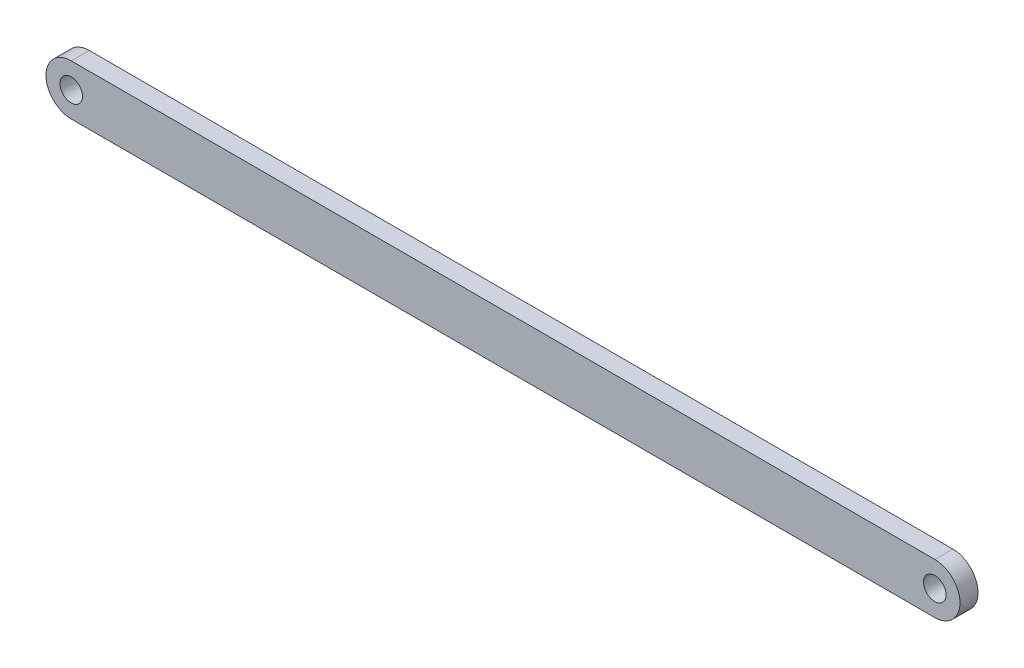
SolidWorks part; units mm, degrees
ref_plane "Front Plane" through (0, 0, 0) normal (0, 0, 1) x (1, 0, 0)
ref_plane "Top Plane" through (0, 0, 0) normal (0, 1, 0) x (1, 0, 0)
ref_plane "Right Plane" through (0, 0, 0) normal (1, 0, 0) x (0, 0, -1)
sketch "Sketch1" plane through (0, 0, 0) normal (0, 0, 1) x (1, 0, 0)
  line L1 (-76.2, 4.445) -> (76.2, 4.445)
  line L2 (-76.2, 4.445) -> (-76.2, -4.445)
  line L3 (-76.2, -4.445) -> (76.2, -4.445)
  line L4 (76.2, 4.445) -> (76.2, -4.445)
  line L5 (-76.2, 4.445) -> (76.2, -4.445) construction
  line L6 (-76.2, -4.445) -> (76.2, 4.445) construction
  circle A0 centre (-76.2, 0) radius 4.445
  circle A1 centre (76.2, 0) radius 4.445
  circle A2 centre (-76.2, 0) radius 1.9939
  circle A3 centre (76.2, 0) radius 1.9939
  point P0 (0, 0)
  point P11 (-76.2, 0)
  point P13 (76.2, 0)
  dimension "D3" = 8.89
  dimension "D4" = 8.89
  dimension "D5" = 3.9878
  dimension "D6" = 3.9878
  dimension "D1" = 8.89
  dimension "D2" = 152.4
extrude "Boss-Extrude1" add sketch "Sketch1" along normal blind 3.175 contours A1 L1 A0 L3 | A2 L2 A0 | A2 L2 A0 | A3 L4 A1 | A3 L4 A1
